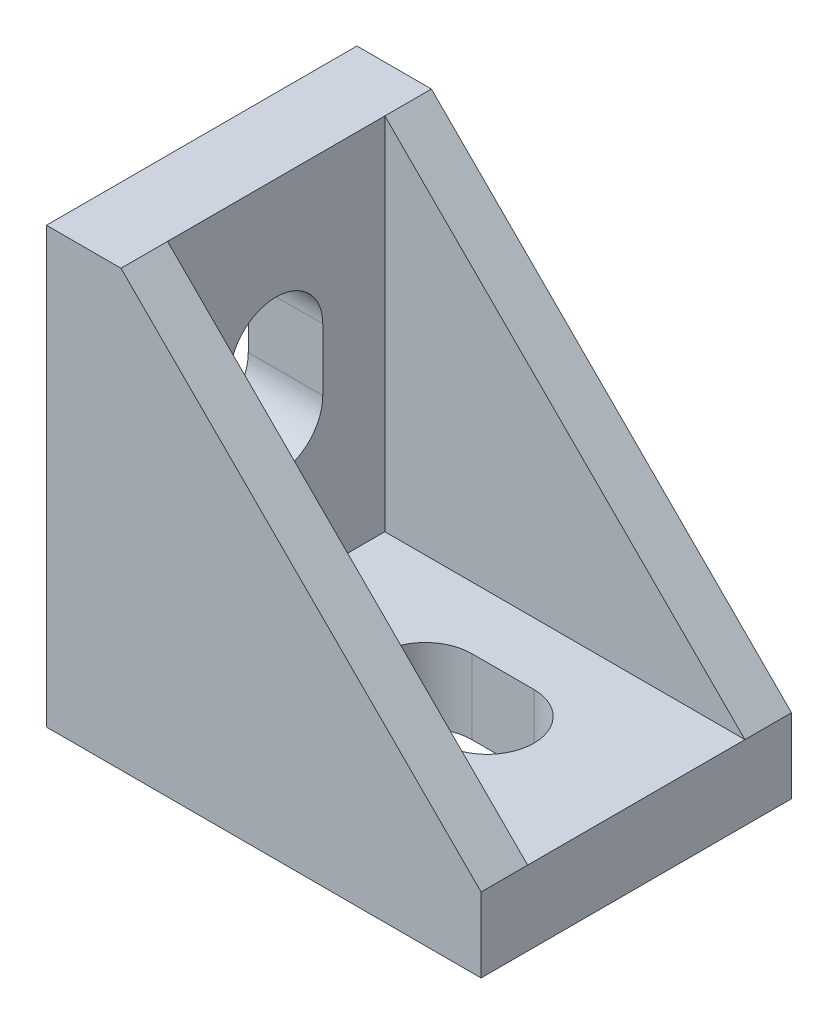
SolidWorks part; units mm, degrees
ref_plane "Front Plane" through (0, 0, 0) normal (0, 0, 1) x (1, 0, 0)
ref_plane "Top Plane" through (0, 0, 0) normal (0, 1, 0) x (1, 0, 0)
ref_plane "Right Plane" through (0, 0, 0) normal (1, 0, 0) x (0, 0, -1)
sketch "Sketch1" plane through (0, 0, 0) normal (0, 1, 0) x (1, 0, 0)
  line L1 (-14, -10) -> (14, -10)
  line L2 (-14, -10) -> (-14, 10)
  line L3 (-14, 10) -> (14, 10)
  line L4 (14, -10) -> (14, 10)
  line L5 (-14, -10) -> (14, 10) construction
  line L6 (-14, 10) -> (14, -10) construction
  point P0 (0, 0)
  dimension "D1" = 28
  dimension "D2" = 20
extrude "Boss-Extrude1" add sketch "Sketch1" along normal blind 4.8
sketch "Sketch2" plane through (-14, 0, 0) normal (-1, 0, 0) x (0, 0, 1)
  line L1 (-10, 0) -> (10, 0)
  line L2 (-10, 0) -> (-10, 28)
  line L3 (-10, 28) -> (10, 28)
  line L4 (10, 0) -> (10, 28)
  dimension "D1" = 28
  dimension "D2" = 20
extrude "Boss-Extrude2" add sketch "Sketch2" against normal blind 4.8
sketch "Sketch3" plane through (-9.2, 0, 0) normal (1, 0, 0) x (0, 0, -1)
  line L0 (0, 18.4) -> (0, 14.4) construction
  line L1 (3, 18.4) -> (3, 14.4)
  line L2 (-3, 18.4) -> (-3, 14.4)
  line L3 (-10, 28) -> (10, 28) construction
  arc A0 (3, 18.4) -> (-3, 18.4) centre (0, 18.4) ccw
  arc A1 (-3, 14.4) -> (3, 14.4) centre (0, 14.4) ccw
  point P3 (0, 16.4)
  dimension "D1" = 4
  dimension "D3" = 3
  dimension "D2" = 11.6
extrude "Cut-Extrude1" cut sketch "Sketch3" against normal through all
sketch "Sketch4" plane through (0, 4.8, 0) normal (0, 1, 0) x (1, 0, 0)
  line L0 (0.4, 0) -> (4.4, 0) construction
  line L1 (0.4, 3) -> (4.4, 3)
  line L2 (0.4, -3) -> (4.4, -3)
  line L3 (14, -10) -> (14, 10) construction
  arc A0 (0.4, 3) -> (0.4, -3) centre (0.4, 0) ccw
  arc A1 (4.4, -3) -> (4.4, 3) centre (4.4, 0) ccw
  point P3 (2.4, 0)
  dimension "D1" = 11.6
  dimension "D3" = 3
  dimension "D2" = 4
extrude "Cut-Extrude2" cut sketch "Sketch4" against normal through all
sketch "Sketch5" plane through (0, 0, 10) normal (0, 0, 1) x (1, 0, 0)
  line L0 (-9.2, 28) -> (14, 4.8)
  line L1 (14, 4.8) -> (-9.2, 4.8)
  line L2 (-9.2, 4.8) -> (-9.2, 28)
extrude "Boss-Extrude3" add sketch "Sketch5" against normal blind 3
sketch "Sketch6" plane through (0, 0, -10) normal (0, 0, -1) x (-1, 0, 0)
  line L0 (9.2, 28) -> (9.2, 4.8)
  line L1 (9.2, 4.8) -> (-14, 4.8)
  line L2 (-14, 4.8) -> (-14, 0) construction
  line L3 (-14, 4.8) -> (9.2, 4.8) construction
  line L4 (-14, 4.8) -> (9.2, 28)
extrude "Boss-Extrude4" add sketch "Sketch6" against normal blind 3
equation "\"D2@Sketch3\"=(28-4.8)/2"
equation "\"D1@Sketch4\"=(28-4.8)/2"
